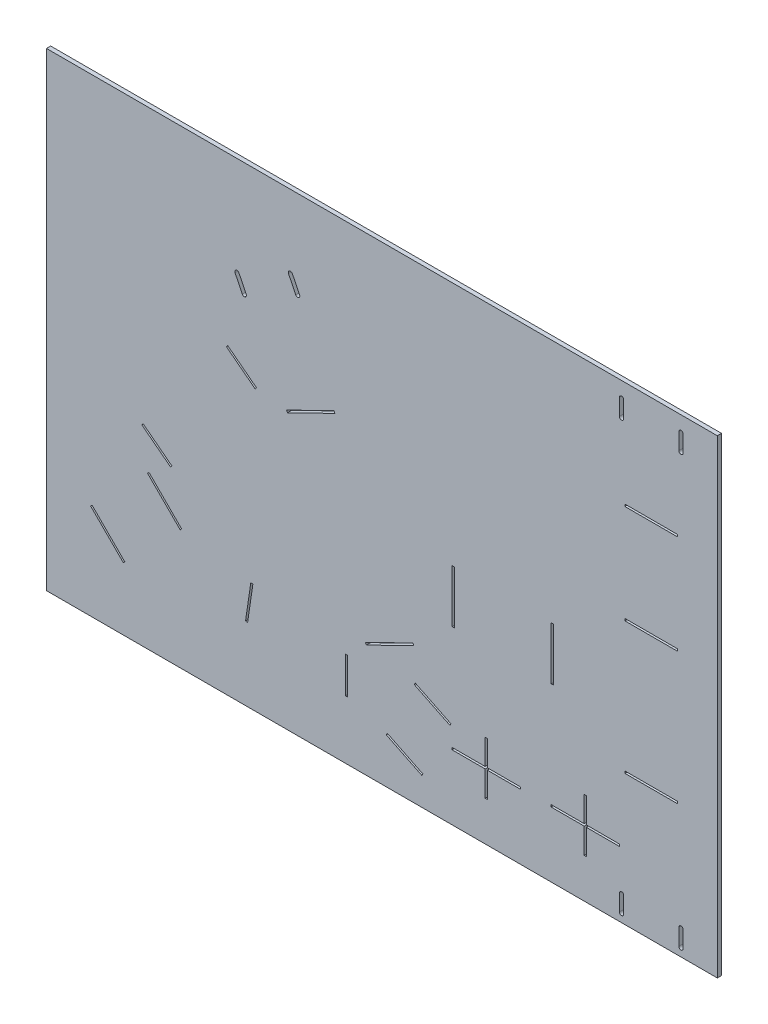
SolidWorks part; units mm, degrees
material "FiberBoard"
ref_plane "Front Plane" through (0, 0, 0) normal (0, 0, 1) x (1, 0, 0)
ref_plane "Top Plane" through (0, 0, 0) normal (0, 1, 0) x (1, 0, 0)
ref_plane "Right Plane" through (0, 0, 0) normal (1, 0, 0) x (0, 0, -1)
sketch "Sketch1" plane through (0, 0, 0) normal (0, 0, 1) x (1, 0, 0)
  line L1 (0, 0) -> (1016, 0)
  line L2 (0, 0) -> (0, -711.2)
  line L3 (0, -711.2) -> (1016, -711.2)
  line L4 (1016, 0) -> (1016, -711.2)
  dimension "D1" = 1016
  dimension "D2" = 711.2
extrude "Boss-Extrude1" add sketch "Sketch1" along normal blind 6.35
sketch "Sketch2" plane through (0, 0, 6.35) normal (0, 0, 1) x (1, 0, 0)
  line L0 (916, -61.2) -> (916, -661.2) construction
  line L1 (1016, -711.2) -> (1016, 0) construction
  line L2 (871, -673.7) -> (871, -698.7) construction
  line L3 (0, -711.2) -> (1016, -711.2) construction
  line L4 (916, -611.2) -> (563.5465, -611.2) construction
  line L5 (916, -411.2) -> (466, -411.2) construction
  line L6 (348.7447, -170.7909) -> (563.5465, -611.2) construction
  line L7 (297.841, -157.6698) -> (369.7445, -122.6001) construction
  line L8 (876, -34.6125) -> (956, -34.6125) construction
  line L9 (876, -34.6125) -> (876, -37.7875) construction
  line L10 (876, -37.7875) -> (956, -37.7875) construction
  line L11 (956, -34.6125) -> (956, -37.7875) construction
  line L12 (876, -159.6125) -> (956, -159.6125)
  line L13 (876, -159.6125) -> (876, -162.7875)
  line L14 (876, -162.7875) -> (956, -162.7875)
  line L15 (956, -159.6125) -> (956, -162.7875)
  line L16 (876, -309.6125) -> (956, -309.6125)
  line L17 (876, -309.6125) -> (876, -312.7875)
  line L18 (876, -312.7875) -> (956, -312.7875)
  line L19 (956, -309.6125) -> (956, -312.7875)
  line L20 (876, -509.6125) -> (956, -509.6125)
  line L21 (876, -509.6125) -> (876, -512.7875)
  line L22 (876, -512.7875) -> (956, -512.7875)
  line L23 (956, -509.6125) -> (956, -512.7875)
  line L24 (876, -684.6125) -> (956, -684.6125) construction
  line L25 (876, -684.6125) -> (876, -687.7875) construction
  line L26 (876, -687.7875) -> (956, -687.7875) construction
  line L27 (956, -684.6125) -> (956, -687.7875) construction
  line L32 (764.4125, -371.2) -> (767.5875, -371.2)
  line L33 (764.4125, -371.2) -> (764.4125, -451.2)
  line L34 (764.4125, -451.2) -> (767.5875, -451.2)
  line L35 (767.5875, -371.2) -> (767.5875, -451.2)
  line L36 (764.4125, -371.2) -> (767.5875, -451.2) construction
  line L37 (764.4125, -451.2) -> (767.5875, -371.2) construction
  line L38 (614.4125, -371.2) -> (617.5875, -371.2)
  line L39 (614.4125, -371.2) -> (614.4125, -451.2)
  line L40 (614.4125, -451.2) -> (617.5875, -451.2)
  line L41 (617.5875, -371.2) -> (617.5875, -451.2)
  line L42 (614.4125, -371.2) -> (617.5875, -451.2) construction
  line L43 (614.4125, -451.2) -> (617.5875, -371.2) construction
  line L44 (297.841, -157.6698) -> (299.2328, -160.5235) construction
  line L45 (369.7445, -122.6001) -> (371.1363, -125.4538) construction
  line L46 (299.2328, -160.5235) -> (371.1363, -125.4538) construction
  line L47 (297.841, -157.6698) -> (371.1363, -125.4538) construction
  line L48 (369.7445, -122.6001) -> (299.2328, -160.5235) construction
  line L53 (874.25, -673.7) -> (874.25, -698.7)
  line L54 (867.75, -673.7) -> (867.75, -698.7)
  line L55 (363.5967, -292.4889) -> (435.5002, -257.4192)
  line L56 (363.5967, -292.4889) -> (364.9885, -295.3426)
  line L57 (435.5002, -257.4192) -> (436.892, -260.2729)
  line L58 (364.9885, -295.3426) -> (436.892, -260.2729)
  line L59 (363.5967, -292.4889) -> (436.892, -260.2729) construction
  line L60 (435.5002, -257.4192) -> (364.9885, -295.3426) construction
  line L61 (584.7692, -567.6871) -> (542.3239, -654.7129) construction
  line L62 (483.0617, -537.4286) -> (554.9653, -502.3589)
  line L63 (814.4125, -571.2) -> (817.5875, -571.2)
  line L64 (814.4125, -571.2) -> (814.4125, -651.2)
  line L65 (814.4125, -651.2) -> (817.5875, -651.2)
  line L66 (817.5875, -571.2) -> (817.5875, -651.2)
  line L67 (814.4125, -571.2) -> (817.5875, -651.2) construction
  line L68 (814.4125, -651.2) -> (817.5875, -571.2) construction
  line L69 (664.4125, -571.2) -> (667.5875, -571.2)
  line L70 (664.4125, -571.2) -> (664.4125, -651.2)
  line L71 (664.4125, -651.2) -> (667.5875, -651.2)
  line L72 (667.5875, -571.2) -> (667.5875, -651.2)
  line L73 (664.4125, -571.2) -> (667.5875, -651.2) construction
  line L74 (664.4125, -651.2) -> (667.5875, -571.2) construction
  line L75 (483.0617, -537.4286) -> (484.4536, -540.2823)
  line L76 (554.9653, -502.3589) -> (556.3571, -505.2126)
  line L77 (484.4536, -540.2823) -> (556.3571, -505.2126)
  line L78 (483.0617, -537.4286) -> (556.3571, -505.2126) construction
  line L79 (554.9653, -502.3589) -> (484.4536, -540.2823) construction
  line L80 (558.5013, -553.1092) -> (612.4289, -579.4114)
  line L81 (558.5013, -553.1092) -> (557.1094, -555.9628)
  line L82 (612.4289, -579.4114) -> (611.0371, -582.2651)
  line L83 (557.1094, -555.9628) -> (611.0371, -582.2651)
  line L84 (558.5013, -553.1092) -> (611.0371, -582.2651) construction
  line L85 (612.4289, -579.4114) -> (557.1094, -555.9628) construction
  line L86 (516.056, -640.1349) -> (569.9836, -666.4372)
  line L87 (516.056, -640.1349) -> (514.6641, -642.9886)
  line L88 (569.9836, -666.4372) -> (568.5918, -669.2908)
  line L89 (514.6641, -642.9886) -> (568.5918, -669.2908)
  line L90 (516.056, -640.1349) -> (568.5918, -669.2908) construction
  line L91 (569.9836, -666.4372) -> (514.6641, -642.9886) construction
  line L92 (563.5465, -611.2) -> (126.9976, -556.2) construction
  line L93 (180.0306, -503.167) -> (91.6422, -591.5553) construction
  line L94 (69.1385, -564.5615) -> (118.636, -614.059)
  line L95 (69.1385, -564.5615) -> (66.8935, -566.8066)
  line L96 (118.636, -614.059) -> (116.3909, -616.3041)
  line L97 (66.8935, -566.8066) -> (116.3909, -616.3041)
  line L98 (69.1385, -564.5615) -> (116.3909, -616.3041) construction
  line L99 (118.636, -614.059) -> (66.8935, -566.8066) construction
  line L100 (155.2818, -478.4183) -> (204.7793, -527.9157)
  line L101 (155.2818, -478.4183) -> (153.0368, -480.6633)
  line L102 (204.7793, -527.9157) -> (202.5342, -530.1608)
  line L103 (153.0368, -480.6633) -> (202.5342, -530.1608)
  line L104 (155.2818, -478.4183) -> (202.5342, -530.1608) construction
  line L105 (204.7793, -527.9157) -> (153.0368, -480.6633) construction
  line L106 (961, -673.7) -> (961, -698.7) construction
  line L107 (964.25, -673.7) -> (964.25, -698.7)
  line L108 (957.75, -673.7) -> (957.75, -698.7)
  line L109 (288.5633, -150.0536) -> (299.5226, -172.5234) construction
  line L110 (291.4844, -148.6289) -> (302.4436, -171.0987)
  line L111 (285.6422, -151.4783) -> (296.6015, -173.9481)
  line L112 (369.4547, -110.6002) -> (380.414, -133.07) construction
  line L113 (372.3758, -109.1755) -> (383.3351, -131.6453)
  line L114 (366.5337, -112.0249) -> (377.4929, -134.4947)
  line L115 (298.5369, -159.0966) -> (294.0429, -161.2885) construction
  line L116 (370.4404, -124.0269) -> (374.9344, -121.8351) construction
  line L117 (871, -23.7) -> (871, -48.7) construction
  line L118 (874.25, -23.7) -> (874.25, -48.7)
  line L119 (867.75, -23.7) -> (867.75, -48.7)
  line L120 (961, -48.7) -> (961, -23.7) construction
  line L121 (957.75, -48.7) -> (957.75, -23.7)
  line L122 (964.25, -48.7) -> (964.25, -23.7)
  arc A0 (874.25, -673.7) -> (867.75, -673.7) centre (871, -673.7) ccw
  arc A1 (867.75, -698.7) -> (874.25, -698.7) centre (871, -698.7) ccw
  arc A2 (964.25, -673.7) -> (957.75, -673.7) centre (961, -673.7) ccw
  arc A3 (957.75, -698.7) -> (964.25, -698.7) centre (961, -698.7) ccw
  arc A4 (291.4844, -148.6289) -> (285.6422, -151.4783) centre (288.5633, -150.0536) ccw
  arc A5 (296.6015, -173.9481) -> (302.4436, -171.0987) centre (299.5226, -172.5234) ccw
  arc A6 (372.3758, -109.1755) -> (366.5337, -112.0249) centre (369.4547, -110.6002) ccw
  arc A7 (377.4929, -134.4947) -> (383.3351, -131.6453) centre (380.414, -133.07) ccw
  arc A8 (874.25, -23.7) -> (867.75, -23.7) centre (871, -23.7) ccw
  arc A9 (867.75, -48.7) -> (874.25, -48.7) centre (871, -48.7) ccw
  arc A10 (957.75, -48.7) -> (964.25, -48.7) centre (961, -48.7) ccw
  arc A11 (964.25, -23.7) -> (957.75, -23.7) centre (961, -23.7) ccw
  point P31 (766, -411.2)
  point P36 (916, -34.6125)
  point P37 (956, -36.2)
  point P38 (956, -161.2)
  point P39 (956, -311.2)
  point P40 (956, -511.2)
  point P41 (956, -686.2)
  point P43 (616, -411.2)
  point P49 (334.4887, -141.5618)
  point P50 (378.3258, -231.4412)
  point P51 (400.2443, -276.3809)
  point P59 (871, -686.2)
  point P61 (563.5465, -611.2)
  point P66 (816, -611.2)
  point P71 (666, -611.2)
  point P78 (519.7094, -521.3206)
  point P79 (542.3239, -654.7129)
  point P85 (584.7692, -567.6871)
  point P86 (91.6422, -591.5553)
  point P95 (92.7647, -590.4328)
  point P96 (180.0306, -503.167)
  point P97 (178.908, -504.2895)
  point P111 (961, -686.2)
  point P116 (876, -686.2)
  point P119 (294.0429, -161.2885)
  point P126 (374.9344, -121.8351)
  point P140 (871, -36.2)
  point P145 (876, -36.2)
  point P148 (961, -36.2)
  dimension "D19" = 3.25
  dimension "D38" = 3.25
  dimension "D42" = 3.25
  dimension "D44" = 5
  dimension "D1" = 600
  dimension "D2" = 100
  dimension "D3" = 50
  dimension "D4" = 50
  dimension "D5" = 450
  dimension "D6" = 200
  dimension "D7" = 64
  dimension "D8" = 490
  dimension "D9" = 80
  dimension "D10" = 3.175
  dimension "D11" = 675
  dimension "D12" = 550
  dimension "D13" = 400
  dimension "D14" = 200
  dimension "D15" = 25
  dimension "D16" = 250
  dimension "D17" = 400
  dimension "D18" = 150
  dimension "D20" = 300
  dimension "D21" = 64
  dimension "D22" = 100
  dimension "D23" = 200
  dimension "D24" = 350
  dimension "D25" = 100
  dimension "D26" = 60
  dimension "D27" = 3.175
  dimension "D28" = 440
  dimension "D29" = 55
  dimension "D30" = 125
  dimension "D31" = 45
  dimension "D32" = 50
  dimension "D33" = 70
  dimension "D34" = 3.175
  dimension "D35" = 25
  dimension "D36" = 5
  dimension "D37" = 5
  dimension "D39" = 25
  dimension "D40" = 5
  dimension "D41" = 25
  dimension "D43" = 5
  dimension "D45" = 90
extrude "Cut-Extrude1" cut sketch "Sketch2" against normal blind 6.35
sketch "Sketch3" plane through (0, 0, 6.35) normal (0, 0, 1) x (1, 0, 0)
  line L0 (817.5875, -651.2) -> (817.5875, -571.2) construction
  line L1 (814.4125, -571.2) -> (814.4125, -651.2) construction
  line L2 (667.5875, -651.2) -> (667.5875, -571.2) construction
  line L3 (664.4125, -571.2) -> (664.4125, -651.2) construction
  line L4 (817.5875, -651.2) -> (817.5875, -571.2) construction
  line L5 (814.4125, -571.2) -> (814.4125, -651.2) construction
  line L6 (667.5875, -651.2) -> (667.5875, -571.2) construction
  line L7 (664.4125, -571.2) -> (664.4125, -651.2) construction
  line L9 (614.4125, -609.6125) -> (664.4125, -609.6125)
  line L10 (614.4125, -609.6125) -> (614.4125, -612.7875)
  line L11 (614.4125, -612.7875) -> (664.4125, -612.7875)
  line L12 (664.4125, -609.6125) -> (664.4125, -612.7875)
  line L13 (614.4125, -609.6125) -> (664.4125, -612.7875) construction
  line L14 (614.4125, -612.7875) -> (664.4125, -609.6125) construction
  line L15 (667.5875, -609.6125) -> (717.5875, -609.6125)
  line L16 (667.5875, -609.6125) -> (667.5875, -612.7875)
  line L17 (667.5875, -612.7875) -> (717.5875, -612.7875)
  line L18 (717.5875, -609.6125) -> (717.5875, -612.7875)
  line L19 (667.5875, -609.6125) -> (717.5875, -612.7875) construction
  line L20 (667.5875, -612.7875) -> (717.5875, -609.6125) construction
  line L21 (764.4125, -609.6125) -> (814.4125, -609.6125)
  line L22 (764.4125, -609.6125) -> (764.4125, -612.7875)
  line L23 (764.4125, -612.7875) -> (814.4125, -612.7875)
  line L24 (814.4125, -609.6125) -> (814.4125, -612.7875)
  line L25 (764.4125, -609.6125) -> (814.4125, -612.7875) construction
  line L26 (764.4125, -612.7875) -> (814.4125, -609.6125) construction
  line L27 (817.5875, -609.6125) -> (867.5875, -609.6125)
  line L28 (817.5875, -609.6125) -> (817.5875, -612.7875)
  line L29 (817.5875, -612.7875) -> (867.5875, -612.7875)
  line L30 (867.5875, -609.6125) -> (867.5875, -612.7875)
  line L31 (817.5875, -609.6125) -> (867.5875, -612.7875) construction
  line L32 (817.5875, -612.7875) -> (867.5875, -609.6125) construction
  point P8 (639.4125, -611.2)
  point P13 (664.4125, -611.2)
  point P14 (692.5875, -611.2)
  point P19 (789.4125, -611.2)
  point P24 (842.5875, -611.2)
  dimension "D1" = 50
  dimension "D2" = 3.175
extrude "Cut-Extrude2" cut sketch "Sketch3" against normal blind 10
sketch "Sketch5" plane through (0, 0, 6.35) normal (0, 0, 1) x (1, 0, 0)
  line L0 (274.5257, -252.511) -> (318.1036, -286.0663)
  line L1 (274.5257, -252.511) -> (272.5886, -255.0266)
  line L2 (318.1036, -286.0663) -> (316.1666, -288.582)
  line L3 (272.5886, -255.0266) -> (316.1666, -288.582)
  line L4 (301.5141, -277.2995) -> (287.2411, -266.3091) construction
  line L5 (287.241, -266.3091) -> (301.526, -277.3086) construction
  point P0 (294.3776, -271.8043)
  point P11 (294.3776, -271.8043)
  dimension "D1" = 3.175
  dimension "D2" = 55
extrude "Cut-Extrude3" cut sketch "Sketch5" against normal through all
sketch "Sketch6" plane through (0, 0, 6.35) normal (0, 0, 1) x (1, 0, 0)
  line L0 (160.8344, -434.1854) -> (171.4982, -442.3966) construction
  line L1 (146.3144, -418.9977) -> (189.8924, -452.5531)
  line L2 (146.3144, -418.9977) -> (144.3774, -421.5134)
  line L3 (189.8924, -452.5531) -> (187.9553, -455.0687)
  line L4 (144.3774, -421.5134) -> (187.9553, -455.0687)
  point P4 (166.1663, -438.291)
  point P7 (166.1663, -438.291)
  dimension "D1" = 55
  dimension "D2" = 3.175
extrude "Cut-Extrude4" cut sketch "Sketch6" against normal through all
sketch "Sketch7" plane through (0, 0, 6.35) normal (0, 0, 1) x (1, 0, 0)
  line L0 (309.933, -564.5465) -> (307.2796, -582.4991) construction
  line L1 (309.4862, -545.8541) -> (301.4446, -600.263)
  line L2 (309.4862, -545.8541) -> (312.6271, -546.3183)
  line L3 (301.4446, -600.263) -> (304.5855, -600.7272)
  line L4 (312.6271, -546.3183) -> (304.5855, -600.7272)
  point P4 (308.6063, -573.5228)
  point P7 (308.6063, -573.5228)
  dimension "D1" = 55
  dimension "D2" = 3.175
extrude "Cut-Extrude5" cut sketch "Sketch7" against normal through all
sketch "Sketch8" plane through (0, 0, 6.35) normal (0, 0, 1) x (1, 0, 0)
  line L0 (455.9649, -581.5973) -> (455.9649, -609.128) construction
  line L1 (452.7899, -567.8627) -> (452.7899, -622.8627)
  line L2 (452.7899, -567.8627) -> (455.9649, -567.8627)
  line L3 (452.7899, -622.8627) -> (455.9649, -622.8627)
  line L4 (455.9649, -567.8627) -> (455.9649, -622.8627)
  point P4 (455.9649, -595.3627)
  point P7 (455.9649, -595.3627)
  dimension "D1" = 55
  dimension "D2" = 3.175
extrude "Cut-Extrude6" cut sketch "Sketch8" against normal through all
